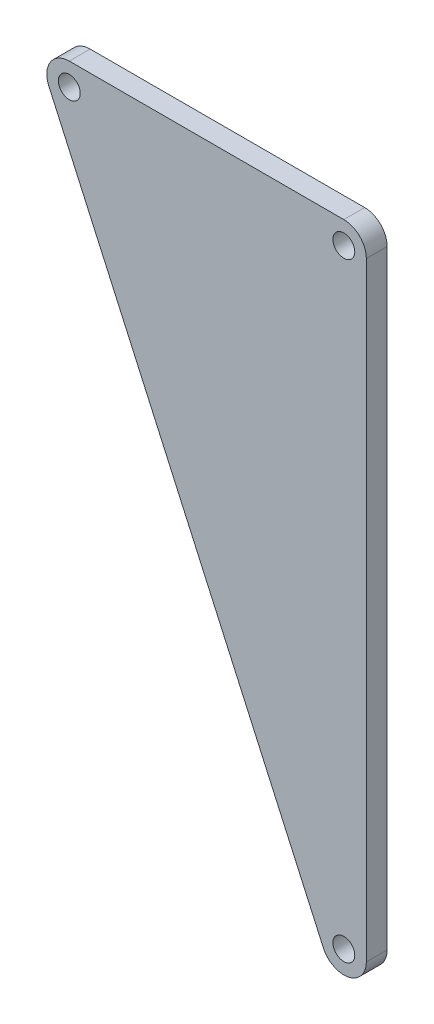
SolidWorks part; units mm, degrees
ref_plane "Front Plane" through (0, 0, 0) normal (0, 0, 1) x (1, 0, 0)
ref_plane "Top Plane" through (0, 0, 0) normal (0, 1, 0) x (1, 0, 0)
ref_plane "Right Plane" through (0, 0, 0) normal (1, 0, 0) x (0, 0, -1)
sketch "Sketch1" plane through (0, 0, 0) normal (0, 0, 1) x (1, 0, 0)
  line L0 (57.02, -120.9743) -> (57.02, 54.0257) construction
  line L1 (0, 4.32) -> (52.7, 4.32)
  line L2 (57.02, 0) -> (57.02, -116.93)
  line L3 (-3.9385, -1.7751) -> (48.7615, -118.7051)
  circle A0 centre (0, 0) radius 2.1
  circle A1 centre (52.7, 0) radius 2.1
  circle A2 centre (52.7, -116.93) radius 2.1
  circle A3 centre (52.7, 0) radius 4.32
  circle A4 centre (52.7, -116.93) radius 4.32
  circle A5 centre (0, 0) radius 4.32
  point P19 (0, 0)
  point P20 (0, 0)
  dimension "D3" = 4.2
  dimension "D1" = 116.93
  dimension "D2" = 52.7
  dimension "D4" = 4.32
extrude "Boss-Extrude1" add sketch "Sketch1" along normal blind 4 contours A5 L3 A4 L2 A3 L1 | A5 A0 | A3 A1 | A4 A2
